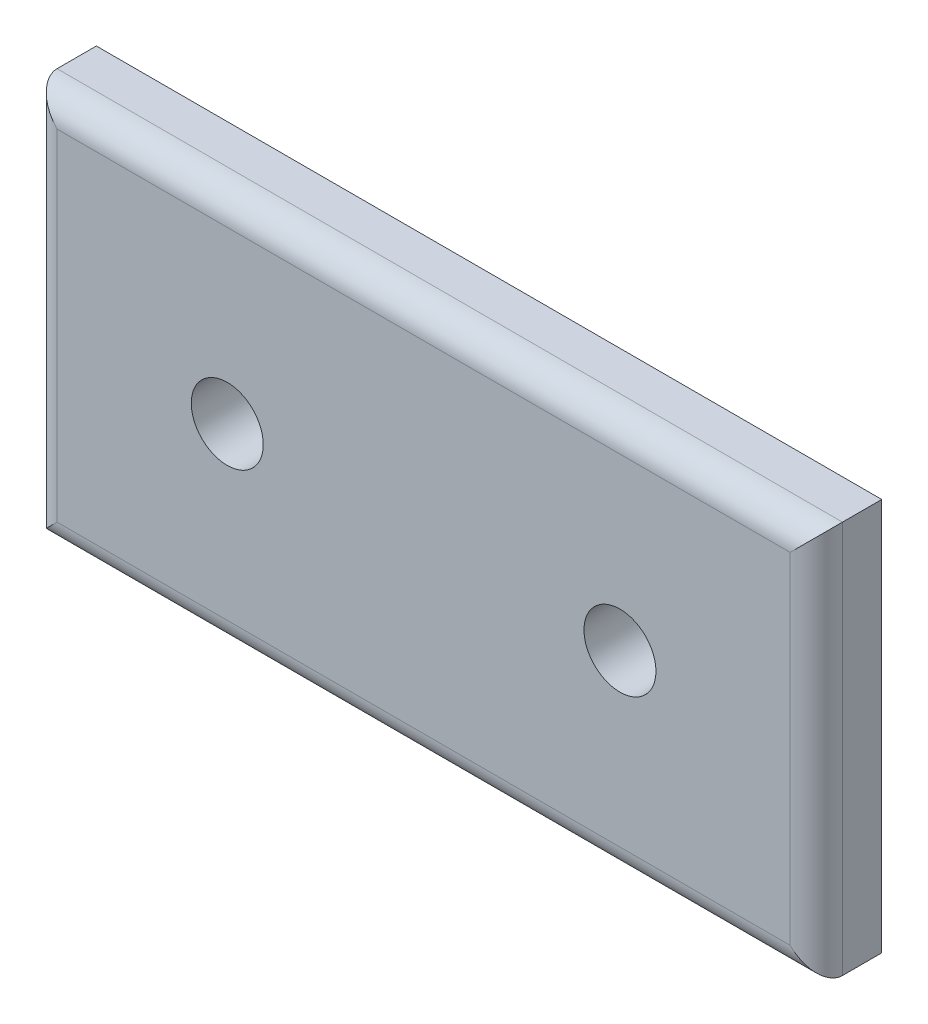
SolidWorks part; units mm, degrees
ref_plane "Front Plane" through (0, 0, 0) normal (0, 0, 1) x (1, 0, 0)
ref_plane "Top Plane" through (0, 0, 0) normal (0, 1, 0) x (1, 0, 0)
ref_plane "Right Plane" through (0, 0, 0) normal (1, 0, 0) x (0, 0, -1)
sketch "Sketch1" plane through (0, 0, 0) normal (0, 0, 1) x (1, 0, 0)
  line L1 (0, 0) -> (76.2, 0)
  line L2 (0, 0) -> (0, 38.1)
  line L3 (0, 38.1) -> (76.2, 38.1)
  line L4 (76.2, 0) -> (76.2, 38.1)
  dimension "D1" = 38.1
  dimension "D2" = 76.2
extrude "Boss-Extrude1" add sketch "Sketch1" along normal blind 6.35
fillet "Fillet1" radius 2.54 4 edges at (38.1, 38.1, 6.35) (76.2, 19.05, 6.35) (38.1, 0, 6.35) (0, 19.05, 6.35)
sketch "Sketch2" plane through (0, 0, 6.35) normal (0, 0, 1) x (1, 0, 0)
  line L0 (0, 19.05) -> (76.2, 19.05) construction
  line L1 (0, 0) -> (0, 38.1) construction
  line L2 (76.2, 38.1) -> (76.2, 0) construction
  circle A0 centre (19.05, 19.05) radius 3.4925
  circle A1 centre (57.15, 19.05) radius 3.4925
  dimension "D1" = 6.985
  dimension "D2" = 6.985
  dimension "D3" = 19.05
  dimension "D4" = 19.05
extrude "Cut-Extrude1" cut sketch "Sketch2" against normal blind 6.35
